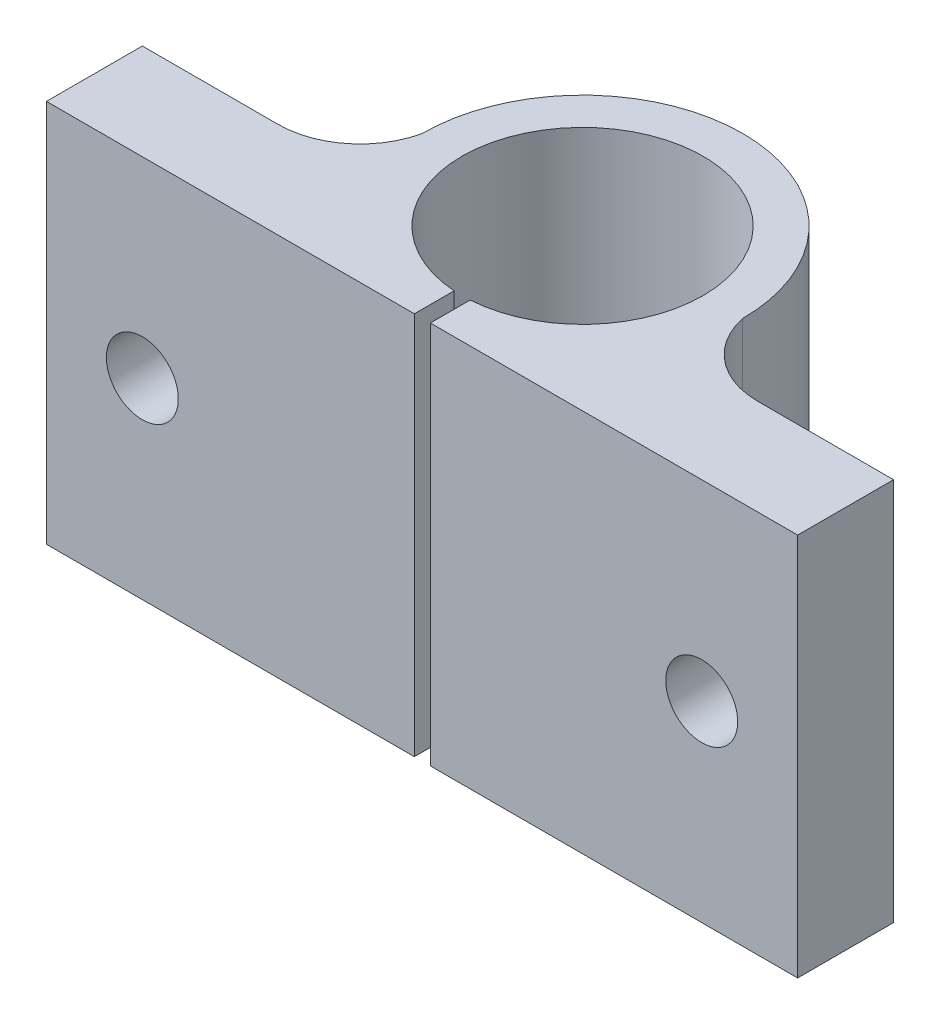
SolidWorks part; units mm, degrees
material "ABS"
ref_plane "Front Plane" through (0, 0, 0) normal (0, 0, 1) x (1, 0, 0)
ref_plane "Top Plane" through (0, 0, 0) normal (0, 1, 0) x (1, 0, 0)
ref_plane "Right Plane" through (0, 0, 0) normal (1, 0, 0) x (0, 0, -1)
ref_plane "Plane1" through (0, 24, 0) normal (0, 1, 0) x (1, 0, 0)
sketch "Sketch1" plane through (0, 24, 0) normal (0, 1, 0) x (1, 0, 0)
  line L0 (0, 0) -> (47, 0)
  line L1 (47, 0) -> (47, 6)
  line L2 (47, 6) -> (38.5, 6)
  line L3 (8.5, 6) -> (0, 6)
  line L4 (0, 6) -> (0, 0)
  arc A0 (38.5, 6) -> (33.5414, 10.0218) centre (38.5, 11.0678) cw
  arc A1 (33.5414, 10.0218) -> (13.4959, 9.9961) centre (23.5186, 10.0227) ccw
  arc A2 (13.4959, 9.9961) -> (8.5, 6) centre (8.5, 11.121) cw
extrude "Boss-Extrude1" add sketch "Sketch1" against normal blind 24
sketch "Sketch2" plane through (0, 0, 0) normal (0, -1, 0) x (1, 0, 0)
  line L0 (24.0186, 0) -> (23.0186, 0)
  line L1 (23.0186, 0) -> (23.0186, -2.4893)
  line L2 (24.0186, -2.4893) -> (24.0186, 0)
  arc A0 (23.0186, -2.4893) -> (24.0186, -2.4893) centre (23.5186, -10.0227) cw
extrude "Cut-Extrude1" cut sketch "Sketch2" against normal through all
ref_plane "Plane2" through (0, 0, -10.0227) normal (0, 0, -1) x (-1, 0, 0)
sketch "Sketch3" plane through (0, 0, -10.0227) normal (0, 0, -1) x (-1, 0, 0)
  line L0 (-31.0686, 0) -> (-23.5186, 0)
  line L1 (-23.5186, 0) -> (-23.5186, 24)
  line L2 (-23.5186, 24) -> (-31.0686, 24)
  line L3 (-31.0686, 24) -> (-31.0686, 0)
  line L4 (-23.5186, 0) -> (-23.5186, 24) construction
revolve "Cut-Revolve1" cut sketch "Sketch3" angle 360 about L4
hole_wizard "Ø4.5 (4.5) Diameter Hole1" positions "Sketch5" profile "Sketch4" hole size "Ø4.5" standard "ANSI Metric" end condition through all
sketch "Sketch5" plane through (0, 0, -6) normal (0, 0, -1) x (-1, 0, 0)
  line L0 (12.4896, 12) -> (-54.1629, 12) construction
  line L2 (-8.5, 0) -> (0, 0) construction
  line L3 (-8.5, 24) -> (0, 24) construction
  line L4 (-23.5, -37.0677) -> (-23.5, 34.9399) construction
  line L6 (0, 0) -> (0, 24) construction
  line L7 (-47, 0) -> (-47, 24) construction
  point P0 (-41, 12)
  point P1 (-6, 12)
  dimension "D1" = 35
sketch "Sketch4" plane through (41, 12, -6) normal (1, 0, 0) x (0, 1, 0)
  line L0 (0, 0) -> (0, 6)
  line L1 (0, 6) -> (2.25, 6)
  line L2 (2.25, 6) -> (2.25, 0)
  line L5 (2.25, 0) -> (0, 0)
  line L11 (0, -6.35) -> (0, 107.95) construction
  dimension "Thru Hole Dia." = 4.5
  dimension "Thru Hole Depth" = 6
